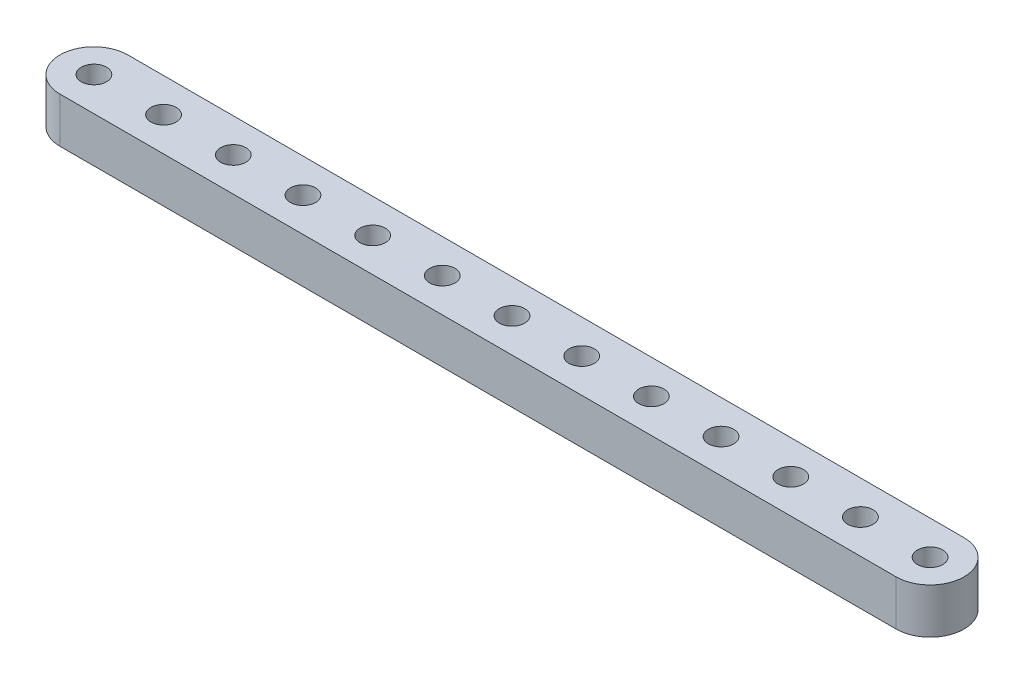
SolidWorks part; units mm, degrees
ref_plane "Front Plane" through (0, 0, 0) normal (0, 0, 1) x (1, 0, 0)
ref_plane "Top Plane" through (0, 0, 0) normal (0, 1, 0) x (1, 0, 0)
ref_plane "Right Plane" through (0, 0, 0) normal (1, 0, 0) x (0, 0, -1)
ref_plane "Plane1" through (0, 0, 0) normal (0, -1, 0) x (1, 0, 0)
sketch "Sketch1" plane through (0, 0, 0) normal (0, -1, 0) x (1, 0, 0)
  line L0 (-58.674, -4.7625) -> (58.674, -4.7625)
  line L1 (58.674, 4.7625) -> (-58.674, 4.7625)
  arc A0 (58.674, -4.7625) -> (58.674, 4.7625) centre (58.674, 0) ccw
  arc A1 (-58.674, 4.7625) -> (-58.674, -4.7625) centre (-58.674, 0) ccw
  circle A2 centre (58.674, 0) radius 1.778
  circle A3 centre (48.895, 0) radius 1.778
  circle A4 centre (39.116, 0) radius 1.778
  circle A5 centre (29.337, 0) radius 1.778
  circle A6 centre (19.558, 0) radius 1.778
  circle A7 centre (9.779, 0) radius 1.778
  circle A8 centre (0, 0) radius 1.778
  circle A9 centre (-9.779, 0) radius 1.778
  circle A10 centre (-19.558, 0) radius 1.778
  circle A11 centre (-29.337, 0) radius 1.778
  circle A12 centre (-39.116, 0) radius 1.778
  circle A13 centre (-48.895, 0) radius 1.778
  circle A14 centre (-58.674, 0) radius 1.778
extrude "Boss-Extrude1" add sketch "Sketch1" against normal blind 6.35
